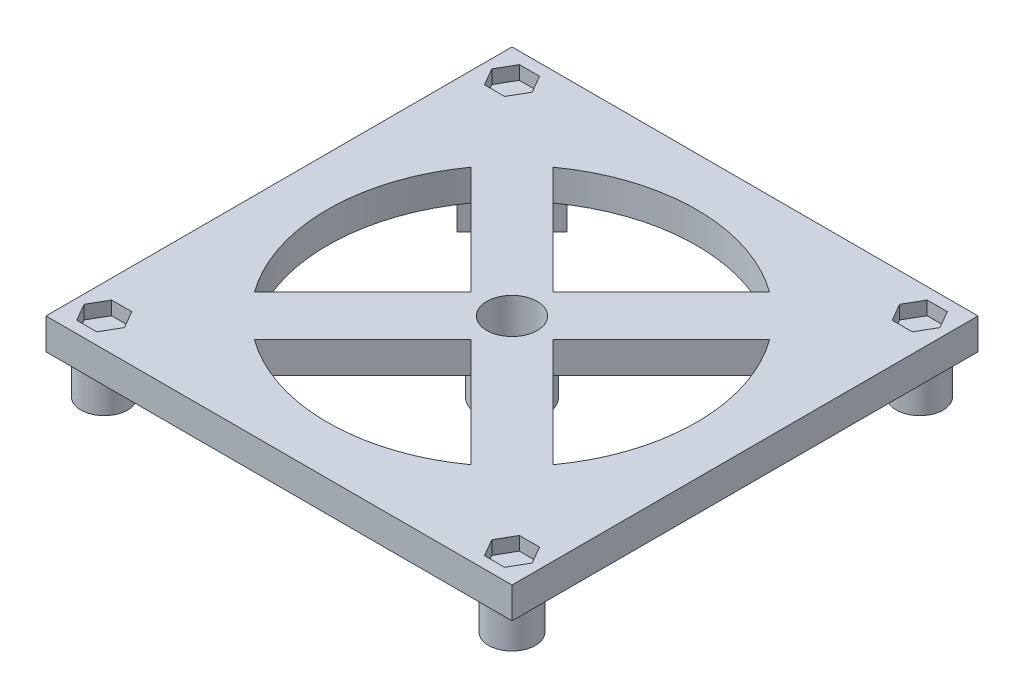
SolidWorks part; units mm, degrees
ref_plane "Front Plane" through (0, 0, 0) normal (0, 0, 1) x (1, 0, 0)
ref_plane "Top Plane" through (0, 0, 0) normal (0, 1, 0) x (1, 0, 0)
ref_plane "Right Plane" through (0, 0, 0) normal (1, 0, 0) x (0, 0, -1)
sketch "Sketch2" plane through (0, 0, 0) normal (0, 1, 0) x (1, 0, 0)
  line L1 (0, 0) -> (-120, 0)
  line L2 (0, 0) -> (0, -120)
  line L3 (0, -120) -> (-120, -120)
  line L4 (-120, 0) -> (-120, -120)
  dimension "D2" = 120
extrude "Boss-Extrude1" add sketch "Sketch2" along normal blind 8
sketch "Sketch3" plane through (0, 8, 0) normal (0, 1, 0) x (1, 0, 0)
  line L0 (-120, -120) -> (0, -120) construction
  line L1 (-2.3038, -112.5) -> (-4.9019, -108)
  line L2 (-4.9019, -108) -> (-10.0981, -108)
  line L3 (-10.0981, -108) -> (-12.6962, -112.5)
  line L4 (-12.6962, -112.5) -> (-10.0981, -117)
  line L5 (-10.0981, -117) -> (-4.9019, -117)
  line L6 (-4.9019, -117) -> (-2.3038, -112.5)
  line L7 (0, -120) -> (0, 0) construction
  circle A0 centre (-7.5, -112.5) radius 4.5 construction
  point P12 (-15.9814, -105.2852)
  dimension "D3" = 9
  dimension "D1" = 7.5
  dimension "D2" = 7.5
extrude "Cut-Extrude1" cut sketch "Sketch3" against normal blind 3.5
pattern_linear "LPattern1" count 2 spacing 105 along (-1, 0, 0) count 2 spacing 105 along (0, 0, -1) of "Cut-Extrude1"
sketch "Sketch8" plane through (0, 0, 0) normal (0, -1, 0) x (1, 0, 0)
  line L0 (0, 0) -> (-120, 0) construction
  line L1 (-120, 120) -> (0, 120) construction
  line L2 (-120, 0) -> (-120, 120) construction
  line L3 (-49.3934, 60) -> (-21.5305, 87.8629)
  line L4 (-32.1371, 21.5305) -> (-60, 49.3934)
  line L6 (-21.5305, 32.1371) -> (-49.3934, 60)
  line L9 (-87.8629, 21.5305) -> (-60, 49.3934)
  line L11 (-98.4695, 32.1371) -> (-70.6066, 60)
  line L12 (-60, 70.6066) -> (-32.1371, 98.4695)
  line L13 (-70.6066, 60) -> (-98.4695, 87.8629)
  line L14 (-60, 70.6066) -> (-87.8629, 98.4695)
  line L15 (-60, 60) -> (-74.2771, 74.2771) construction
  line L16 (-60, 60) -> (-66.5571, 53.4429) construction
  line L17 (-60, 60) -> (-68.0921, 60) construction
  circle A0 centre (-60, 60) radius 60 construction
  arc A1 (-98.4695, 87.8629) -> (-98.4695, 32.1371) centre (-60, 60) ccw
  arc A2 (-21.5305, 32.1371) -> (-21.5305, 87.8629) centre (-60, 60) ccw
  arc A3 (-87.8629, 21.5305) -> (-32.1371, 21.5305) centre (-60, 60) ccw
  arc A4 (-32.1371, 98.4695) -> (-87.8629, 98.4695) centre (-60, 60) ccw
  point P20 (-66.5571, 53.4429)
  dimension "D1" = 95
  dimension "D2" = 15
  dimension "D3" = 15
extrude "air holes" cut sketch "Sketch8" against normal up to next
sketch "Sketch11" plane through (0, 0, 0) normal (0, -1, 0) x (1, 0, 0)
  line L4 (0, 0) -> (0, 120)
  line L5 (0, 120) -> (-120, 120)
  line L6 (-120, 120) -> (-120, 0)
  line L7 (-120, 0) -> (0, 0)
  line L8 (0, 0) -> (0, 120)
  line L9 (0, 120) -> (-120, 120)
  line L10 (-120, 120) -> (-120, 0)
  line L11 (-120, 0) -> (0, 0)
  circle A0 centre (-60, 60) radius 8.5
  arc A1 (-98.4695, 87.8629) -> (-98.4695, 32.1371) centre (-60, 60) ccw construction
  dimension "D2" = 17
  dimension "D1" = 0
sketch "Sketch13" plane through (0, 0, 0) normal (0, -1, 0) x (1, 0, 0)
  line L0 (-18.6343, 18.6343) -> (-60, 60) construction
  line L1 (-16.1594, 30.3015) -> (-11.5632, 25.7053)
  line L2 (-16.1594, 30.3015) -> (-30.3015, 16.1594)
  line L3 (-30.3015, 16.1594) -> (-25.7053, 11.5632)
  line L4 (-11.5632, 25.7053) -> (-25.7053, 11.5632)
  line L5 (-60, 60) -> (-31.8944, 60) construction
  arc A0 (-32.1371, 98.4695) -> (-87.8629, 98.4695) centre (-60, 60) ccw construction
  point P6 (-60, 60)
  point P7 (-31.8944, 60)
  point P8 (-11.9146, 26.0342)
  dimension "D1" = 20
  dimension "D2" = 52
  dimension "D3" = 6.5
  dimension "D4" = 45
extrude "heater_mounts" add sketch "Sketch13" along normal blind 10
sketch "Sketch14" plane through (-23.2304, 0, 23.2304) normal (-0.7071, 0, 0.7071) x (0.7071, 0, 0.7071)
  line L0 (0, -5) -> (61.398, -5) construction
  line L1 (0, -5) -> (0, -7.588) construction
  line L2 (10, 0) -> (-10, 0) construction
  line L3 (10, -10) -> (-10, -10) construction
  line L4 (10, -10) -> (10, 0) construction
  line L5 (-10, -10) -> (-10, 0) construction
  circle A0 centre (0, -5) radius 3
  dimension "D1" = 6
extrude "heater_holes" cut sketch "Sketch14" against normal up to next (6.5 mm away)
pattern_circular "CirPattern2" count 4 over 360 about axis through (-60, 0, 60) along (0, 1, 0) of "heater_holes", "heater_mounts"
extrude "Boss-Extrude3" add sketch "Sketch11" along normal blind 10 contours A0
sketch "Sketch16" plane through (0, -10, 0) normal (0, -1, 0) x (1, 0, 0)
  circle A0 centre (-60, 60) radius 6.5
  circle A1 centre (-60, 60) radius 8.5 construction
  dimension "D1" = 13
extrude "Cut-Extrude9" cut sketch "Sketch16" against normal up to next
sketch "Sketch17" plane through (0, 0, 0) normal (0, -1, 0) x (1, 0, 0)
  line L0 (-120, 120) -> (0, 120) construction
  line L1 (-120, 0) -> (-120, 120) construction
  circle A0 centre (-112.5, 112.5) radius 6
  dimension "D1" = 7.5
  dimension "D2" = 7.5
  dimension "D3" = 12
extrude "Boss-Extrude4" add sketch "Sketch17" along normal up to surface (10 mm away) up to face at (-99.0676, -10, 99.0676)
sketch "Sketch18" plane through (0, -10, 0) normal (0, -1, 0) x (1, 0, 0)
  line L1 (-117.4075, 112.5) -> (-114.9537, 108.25)
  line L2 (-114.9537, 108.25) -> (-110.0463, 108.25)
  line L3 (-110.0463, 108.25) -> (-107.5925, 112.5)
  line L4 (-107.5925, 112.5) -> (-110.0463, 116.75)
  line L5 (-110.0463, 116.75) -> (-114.9537, 116.75)
  line L6 (-114.9537, 116.75) -> (-117.4075, 112.5)
  circle A0 centre (-112.5, 112.5) radius 4.25 construction
  circle A1 centre (-112.5, 112.5) radius 6 construction
  dimension "D1" = 8.5
extrude "Cut-Extrude10" cut sketch "Sketch18" against normal blind 3.5 contours L1 L2 L3 L4 L5 L6
pattern_linear "LPattern4" count 2 spacing 105 along (1, 0, 0) count 2 spacing 105 along (0, 0, -1) of "Boss-Extrude4", "Cut-Extrude10"
equation "\"D2@Sketch3\"=\"D1@Sketch3\""
equation "\"D1@Sketch3\"=(120-105)/2"
equation "\"resistor_hole\"=3"
equation "\"D3@Sketch8\"=\"D2@Sketch8\""
equation "\"bearing_od\"=17"
equation "\"D2@Sketch11\"=\"bearing_od\""
equation "\"D2@Sketch17\"=\"D1@Sketch17\""
